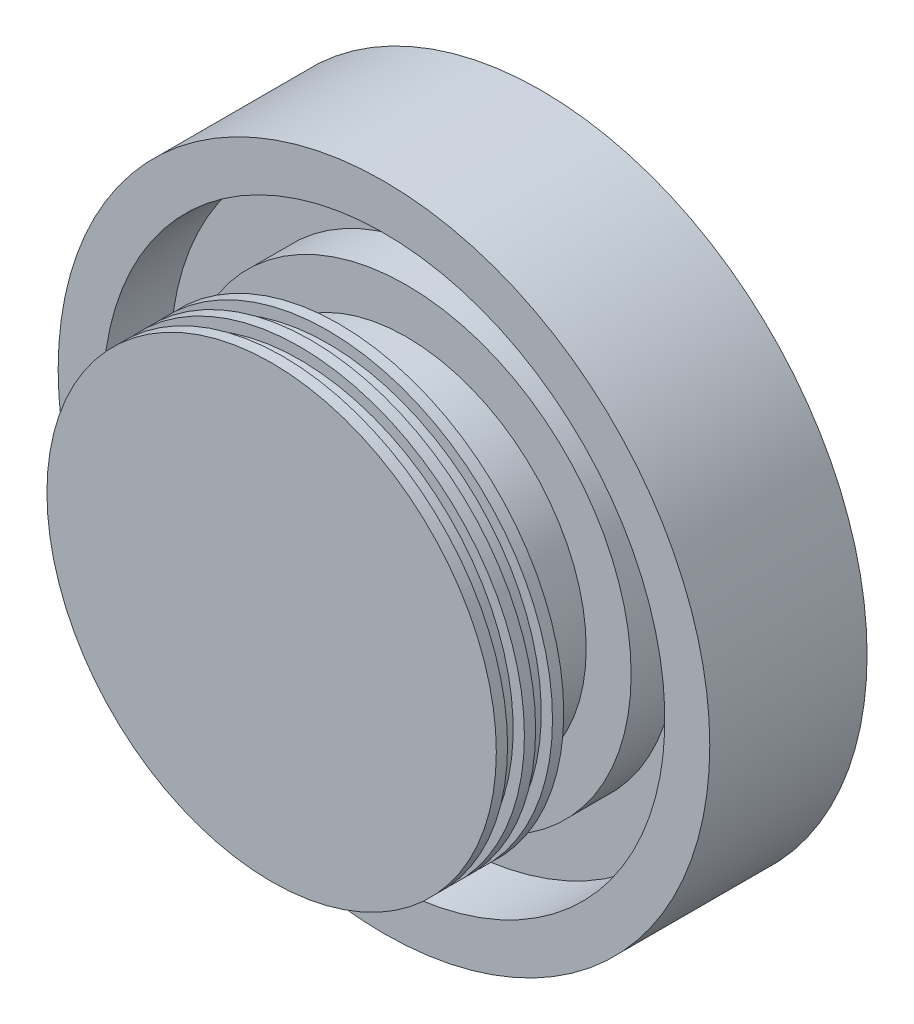
SolidWorks part; units mm, degrees
material "6061 Alloy"
ref_plane "Front Plane" through (0, 0, 0) normal (0, 0, 1) x (1, 0, 0)
ref_plane "Top Plane" through (0, 0, 0) normal (0, 1, 0) x (1, 0, 0)
ref_plane "Right Plane" through (0, 0, 0) normal (1, 0, 0) x (0, 0, -1)
sketch "Sketch1" plane through (0, 0, 0) normal (0, 1, 0) x (1, 0, 0)
  line L0 (0, 0) -> (63.5, 0)
  line L1 (63.5, 0) -> (63.5, 3.175)
  line L2 (63.5, 3.175) -> (60.325, 3.175)
  line L3 (60.325, 3.175) -> (60.325, 7.9375)
  line L4 (60.325, 7.9375) -> (63.5, 7.9375)
  line L5 (63.5, 7.9375) -> (63.5, 11.1125)
  line L6 (63.5, 11.1125) -> (60.325, 11.1125)
  line L7 (60.325, 11.1125) -> (60.325, 15.875)
  line L8 (60.325, 15.875) -> (63.5, 15.875)
  line L9 (63.5, 15.875) -> (63.5, 19.05)
  line L10 (63.5, 19.05) -> (50.8, 19.05)
  line L11 (50.8, 19.05) -> (50.8, 38.1)
  line L12 (50.8, 38.1) -> (63.5, 38.1)
  line L13 (63.5, 38.1) -> (63.5, 50.8)
  line L14 (63.5, 50.8) -> (79.375, 50.8)
  line L15 (79.375, 50.8) -> (79.375, 31.75)
  line L24 (79.375, 31.75) -> (92.075, 31.75)
  line L25 (92.075, 31.75) -> (92.075, 76.2)
  line L28 (12.7, 76.2) -> (12.7, 63.5)
  line L29 (12.7, 63.5) -> (38.1, 63.5)
  line L30 (38.1, 63.5) -> (38.1, 44.45)
  line L31 (38.1, 44.45) -> (0, 44.45)
  line L32 (0, 44.45) -> (0, 0)
  line L33 (12.7, 76.2) -> (92.075, 76.2)
  dimension "D1" = 63.5
  dimension "D2" = 15.875
  dimension "D3" = 3.175
  dimension "D4" = 4.7625
  dimension "D5" = 3.175
  dimension "D6" = 19.05
  dimension "D7" = 12.7
  dimension "D8" = 12.7
  dimension "D9" = 12.7
  dimension "D10" = 12.7
  dimension "D11" = 76.2
  dimension "D12" = 38.1
  dimension "D13" = 12.7
  dimension "D14" = 19.05
  dimension "D15" = 19.05
revolve "Revolve1" add sketch "Sketch1" angle 360 about L32
